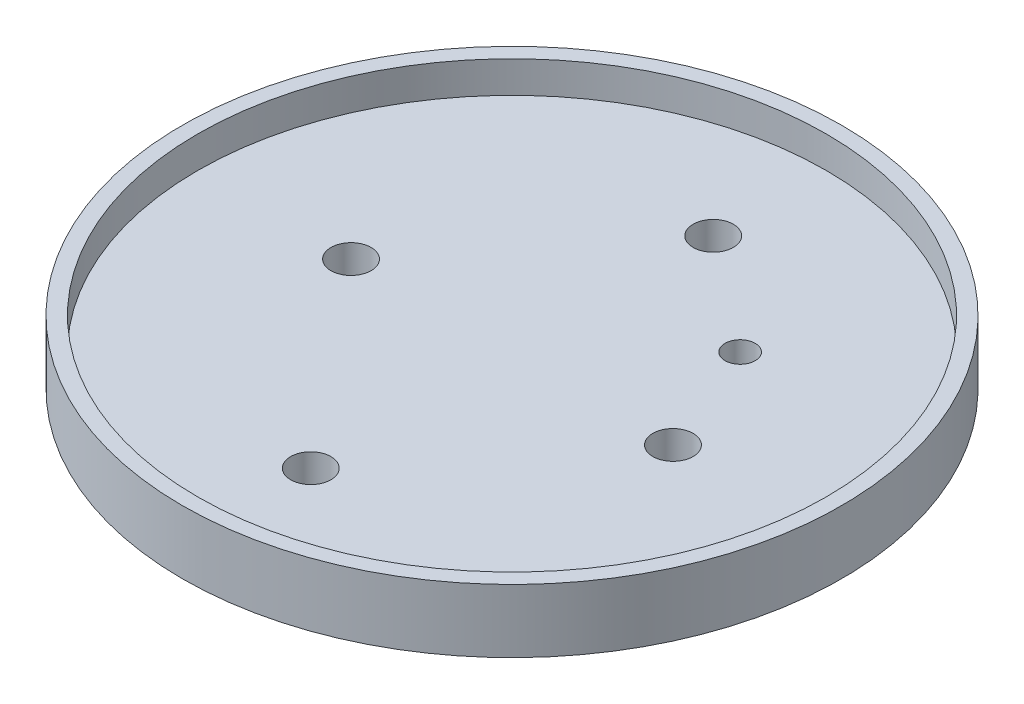
SolidWorks part; units mm, degrees
ref_plane "Front Plane" through (0, 0, 0) normal (0, 0, 1) x (1, 0, 0)
ref_plane "Top Plane" through (0, 0, 0) normal (0, 1, 0) x (1, 0, 0)
ref_plane "Right Plane" through (0, 0, 0) normal (1, 0, 0) x (0, 0, -1)
sketch "Sketch1" plane through (0, 0, 0) normal (0, 1, 0) x (1, 0, 0)
  circle A0 centre (0, 0) radius 52
  circle A1 centre (25.4, 0) radius 3.175
  circle A2 centre (0, 31.75) radius 3.175
  circle A3 centre (-25.4, 0) radius 3.175
  circle A4 centre (0, -31.75) radius 3.175
  circle A5 centre (18, 18) radius 2.38
  dimension "D1" = 104
  dimension "D2" = 6.35
  dimension "D3" = 6.35
  dimension "D4" = 6.35
  dimension "D5" = 6.35
  dimension "D6" = 25.4
  dimension "D7" = 25.4
  dimension "D8" = 31.75
  dimension "D10" = 4.76
  dimension "D11" = 18
  dimension "D12" = 18
  dimension "D9" = 31.75
extrude "Boss-Extrude1" add sketch "Sketch1" along normal blind 5
sketch "Sketch2" plane through (0, 5, 0) normal (0, 1, 0) x (1, 0, 0)
  circle A0 centre (0, 0) radius 52
  circle A1 centre (0, 0) radius 49.6
  dimension "D1" = 99.2
extrude "Boss-Extrude2" add sketch "Sketch2" along normal blind 5
